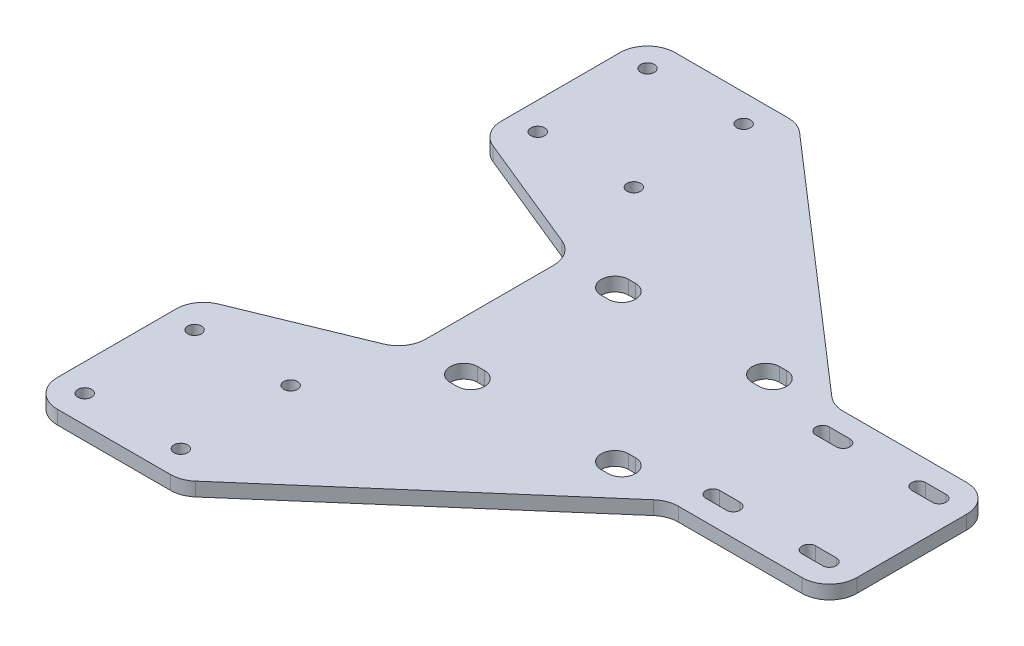
SolidWorks part; units mm, degrees
material "6061-O (SS)"
ref_plane "Plan de face" through (0, 0, 0) normal (0, 0, 1) x (1, 0, 0)
ref_plane "Plan de dessus" through (0, 0, 0) normal (0, 1, 0) x (1, 0, 0)
ref_plane "Plan de droite" through (0, 0, 0) normal (1, 0, 0) x (0, 0, -1)
sketch "Esquisse1" plane through (0, 0, 0) normal (0, 1, 0) x (1, 0, 0)
  line L1 (41.75, -45) -> (-41.75, -45)
  line L2 (41.75, -45) -> (41.75, 45)
  line L3 (41.75, 45) -> (-41.75, 45)
  line L4 (-41.75, -45) -> (-41.75, 45)
  line L5 (41.75, -45) -> (-41.75, 45) construction
  line L6 (41.75, 45) -> (-41.75, -45) construction
  point P0 (0, 0)
  dimension "D1" = 90
  dimension "D2" = 83.5
extrude "Boss.-Extru.1" add sketch "Esquisse1" along normal blind 2
sketch "Esquisse2" plane through (0, 0, 0) normal (0, 1, 0) x (1, 0, 0)
  line L0 (-41.75, -45) -> (41.75, -45) construction
  line L1 (-37.75, -25) -> (-23.75, -25) construction
  line L2 (-37.75, -25) -> (-37.75, -41) construction
  line L3 (-37.75, -41) -> (-23.75, -41) construction
  line L4 (-23.75, -25) -> (-23.75, -41) construction
  line L5 (-37.75, -25) -> (-23.75, -41) construction
  line L6 (-37.75, -41) -> (-23.75, -25) construction
  line L7 (-41.75, 45) -> (-41.75, -45) construction
  line L8 (0, 0) -> (-41.75, 0) construction
  line L9 (-37.75, 41) -> (-23.75, 25) construction
  line L10 (-37.75, 25) -> (-23.75, 41) construction
  line L11 (-23.75, 25) -> (-23.75, 41) construction
  line L12 (-37.75, 41) -> (-23.75, 41) construction
  line L13 (-37.75, 25) -> (-37.75, 41) construction
  line L14 (-37.75, 25) -> (-23.75, 25) construction
  line L15 (29.25, 0) -> (36.25, 8) construction
  line L16 (22.25, 8) -> (36.25, 8) construction
  line L17 (22.25, 8) -> (22.25, -8) construction
  line L18 (22.25, -8) -> (36.25, -8) construction
  line L19 (36.25, 8) -> (36.25, -8) construction
  line L20 (22.25, 8) -> (29.25, 0) construction
  line L21 (22.25, -8) -> (29.25, 0) construction
  line L22 (29.25, 0) -> (36.25, -8) construction
  line L23 (0, 0) -> (41.75, 0) construction
  line L24 (41.75, -45) -> (41.75, 45) construction
  line L25 (41.75, 12) -> (18.25, 12)
  line L26 (18.25, 12) -> (-19.75, 45)
  line L27 (41.75, 45) -> (-41.75, 45) construction
  line L28 (-19.75, 45) -> (41.75, 45)
  line L29 (41.75, 45) -> (41.75, 12)
  line L30 (41.75, -12) -> (18.25, -12)
  line L31 (41.75, -45) -> (41.75, -12)
  line L32 (-19.75, -45) -> (41.75, -45)
  line L33 (18.25, -12) -> (-19.75, -45)
  line L34 (-41.75, -21) -> (-19.75, -12)
  line L35 (-19.75, -12) -> (-19.75, 12)
  line L36 (-19.75, 12) -> (-41.75, 21)
  line L37 (-41.75, 21) -> (-41.75, -21)
  line L38 (20.75, 8) -> (23.75, 8) construction
  line L39 (20.75, 9) -> (23.75, 9)
  line L40 (20.75, 7) -> (23.75, 7)
  line L41 (37.75, 8) -> (34.75, 8) construction
  line L42 (37.75, 7) -> (34.75, 7)
  line L43 (37.75, 9) -> (34.75, 9)
  line L44 (20.75, -8) -> (23.75, -8) construction
  line L45 (20.75, -7) -> (23.75, -7)
  line L46 (20.75, -9) -> (23.75, -9)
  line L47 (37.75, -8) -> (34.75, -8) construction
  line L48 (37.75, -9) -> (34.75, -9)
  line L49 (37.75, -7) -> (34.75, -7)
  circle A0 centre (-23.75, -25) radius 1
  circle A1 centre (-37.75, -25) radius 1
  circle A2 centre (-37.75, -41) radius 1
  circle A3 centre (-23.75, -41) radius 1
  circle A4 centre (-23.75, 41) radius 1
  circle A5 centre (-37.75, 41) radius 1
  circle A6 centre (-37.75, 25) radius 1
  circle A7 centre (-23.75, 25) radius 1
  arc A12 (20.75, 9) -> (20.75, 7) centre (20.75, 8) ccw
  arc A13 (23.75, 7) -> (23.75, 9) centre (23.75, 8) ccw
  arc A14 (37.75, 7) -> (37.75, 9) centre (37.75, 8) ccw
  arc A15 (34.75, 9) -> (34.75, 7) centre (34.75, 8) ccw
  arc A16 (20.75, -7) -> (20.75, -9) centre (20.75, -8) ccw
  arc A17 (23.75, -9) -> (23.75, -7) centre (23.75, -8) ccw
  arc A18 (37.75, -9) -> (37.75, -7) centre (37.75, -8) ccw
  arc A19 (34.75, -7) -> (34.75, -9) centre (34.75, -8) ccw
  point P0 (-30.75, -33)
  point P25 (-30.75, 33)
  point P26 (29.25, 0)
  point P33 (22.25, 8)
  point P52 (-19.75, 0)
  point P58 (36.25, 8)
  point P65 (22.25, -8)
  point P72 (36.25, -8)
  dimension "D3" = 2
  dimension "D4" = 4
  dimension "D5" = 4
  dimension "D6" = 1
  dimension "D1" = 16
  dimension "D2" = 14
  dimension "D7" = 14
  dimension "D8" = 16
  dimension "D9" = 5.5
  dimension "D10" = 4
  dimension "D11" = 4
  dimension "D12" = 4
  dimension "D13" = 4
  dimension "D14" = 4
  dimension "D15" = 4
  dimension "D16" = 4
  dimension "D17" = 1.5
extrude "Enlèv. mat.-Extru.1" cut sketch "Esquisse2" along normal through all
fillet "Congé1" radius 4 12 edges at (18.25, 1, 12) (41.75, 1, 12) (41.75, 1, -12) (18.25, 1, -12) (-19.75, 1, -45) (-41.75, 1, -45) (-41.75, 1, -21) (-19.75, 1, -12) (-19.75, 1, 12) (-41.75, 1, 21) (-41.75, 1, 45) (-19.75, 1, 45)
sketch "Esquisse3" plane through (0, 0, 0) normal (0, 1, 0) x (1, 0, 0)
  line L0 (-1, 0) -> (0, 0) construction
  line L1 (10, -11) -> (-12, -11) construction
  line L2 (10, -11) -> (10, 11) construction
  line L3 (10, 11) -> (-12, 11) construction
  line L4 (-12, -11) -> (-12, 11) construction
  line L5 (10, -11) -> (-12, 11) construction
  line L6 (10, 11) -> (-12, -11) construction
  line L7 (-12.5, 11) -> (-11.5, 11) construction
  line L8 (-12.5, 13) -> (-11.5, 13)
  line L9 (-12.5, 9) -> (-11.5, 9)
  line L10 (-1, 0) -> (-12, 0) construction
  line L11 (-1, 0) -> (-1, 11) construction
  line L12 (10.5, 11) -> (9.5, 11) construction
  line L13 (10.5, 13) -> (9.5, 13)
  line L14 (10.5, 9) -> (9.5, 9)
  line L15 (10.5, -11) -> (9.5, -11) construction
  line L16 (10.5, -13) -> (9.5, -13)
  line L17 (10.5, -9) -> (9.5, -9)
  line L18 (-12.5, -11) -> (-11.5, -11) construction
  line L19 (-12.5, -13) -> (-11.5, -13)
  line L20 (-12.5, -9) -> (-11.5, -9)
  arc A4 (-12.5, 13) -> (-12.5, 9) centre (-12.5, 11) ccw
  arc A5 (-11.5, 9) -> (-11.5, 13) centre (-11.5, 11) ccw
  arc A6 (10.5, 13) -> (10.5, 9) centre (10.5, 11) cw
  arc A7 (9.5, 9) -> (9.5, 13) centre (9.5, 11) cw
  arc A8 (10.5, -13) -> (10.5, -9) centre (10.5, -11) ccw
  arc A9 (9.5, -9) -> (9.5, -13) centre (9.5, -11) ccw
  arc A10 (-12.5, -13) -> (-12.5, -9) centre (-12.5, -11) cw
  arc A11 (-11.5, -9) -> (-11.5, -13) centre (-11.5, -11) cw
  point P0 (-1, 0)
  point P8 (-12, 11)
  point P22 (10, 11)
  point P29 (10, -11)
  point P36 (-12, -11)
  dimension "D3" = 2
  dimension "D1" = 22
  dimension "D2" = 22
  dimension "D4" = 1
  dimension "D5" = 0.5
extrude "Enlèv. mat.-Extru.2" cut sketch "Esquisse3" along normal through all
